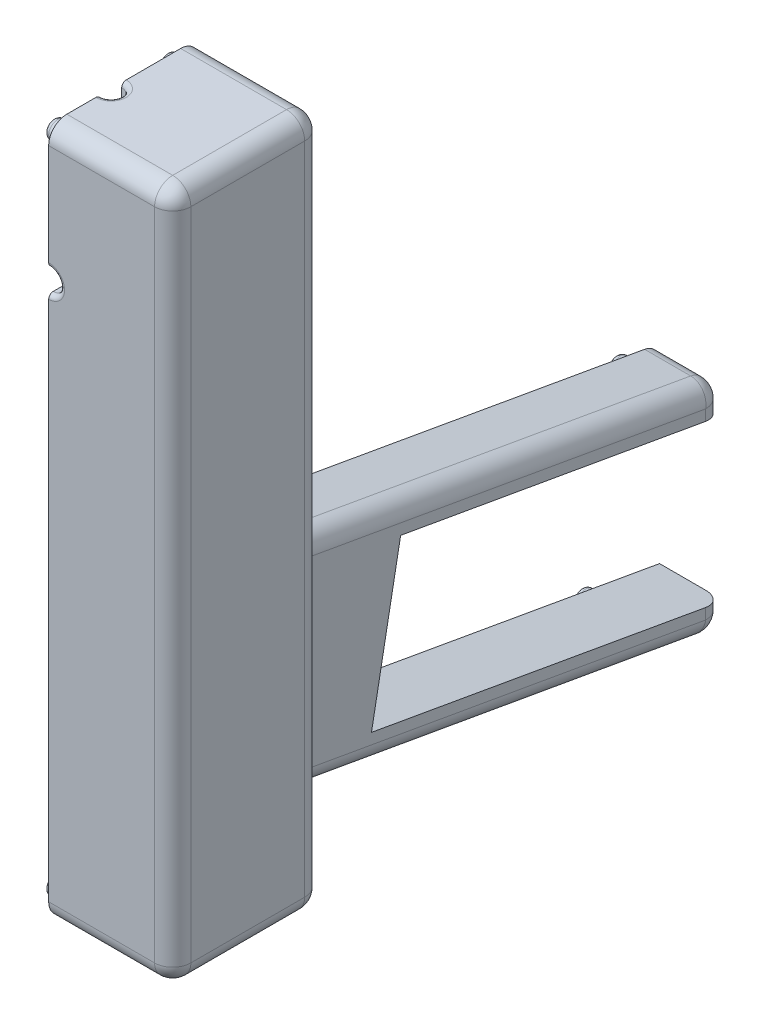
SolidWorks part; units mm, degrees
ref_plane "Front Plane" through (0, 0, 0) normal (0, 0, 1) x (1, 0, 0)
ref_plane "Top Plane" through (0, 0, 0) normal (0, 1, 0) x (1, 0, 0)
ref_plane "Right Plane" through (0, 0, 0) normal (1, 0, 0) x (0, 0, -1)
sketch "Sketch1" plane through (0, 0, 0) normal (0, 1, 0) x (1, 0, 0)
  line L1 (0, 0) -> (27.35, 0)
  line L2 (0, 0) -> (0, 33.1)
  line L3 (0, 33.1) -> (27.35, 33.1)
  line L4 (27.35, 0) -> (27.35, 33.1)
  dimension "D1" = 27.35
  dimension "D2" = 33.1
extrude "Boss-Extrude1" add sketch "Sketch1" along normal blind 152.4
sketch "Sketch2" plane through (0, 0, 0) normal (-1, 0, 0) x (0, 0, 1)
  line L0 (0, 152.4) -> (0, 0) construction
  line L1 (-6.35, 146.05) -> (-26.75, 146.05)
  line L2 (-6.35, 146.05) -> (-6.35, 6.35)
  line L3 (-6.35, 6.35) -> (-26.75, 6.35)
  line L4 (-26.75, 146.05) -> (-26.75, 6.35)
  line L5 (-33.1, 152.4) -> (0, 152.4) construction
  line L6 (-33.1, 152.4) -> (-33.1, 0) construction
  line L7 (-33.1, 0) -> (0, 0) construction
  dimension "D1" = 6.35
  dimension "D2" = 6.35
  dimension "D3" = 6.35
  dimension "D4" = 6.35
extrude "Cut-Extrude1" cut sketch "Sketch2" against normal blind 21
sketch "Sketch3" plane through (0, 0, 0) normal (0, 0, 1) x (1, 0, 0)
  line L0 (0, 152.4) -> (0, 0) construction
  line L1 (0, 125.055) -> (0, 120.055)
  arc A0 (0, 125.055) -> (0, 120.055) centre (0, 122.555) cw
  dimension "D1" = 29.845
extrude "HitLED" cut sketch "Sketch3" against normal up to next
sketch "Sketch6" plane through (21, 0, 0) normal (-1, 0, 0) x (0, 0, 1)
  line L0 (-15.7, 107.95) -> (-15.7, 33.02)
  line L1 (-9.35, 107.95) -> (-23.75, 107.95)
  line L2 (-9.35, 107.95) -> (-9.35, 33.02)
  line L3 (-9.35, 33.02) -> (-23.75, 33.02)
  line L4 (-23.75, 107.95) -> (-23.75, 33.02)
  line L5 (-17.4, 33.02) -> (-17.4, 107.95)
  line L7 (-6.35, 146.05) -> (-26.75, 146.05) construction
  line L8 (-26.75, 146.05) -> (-26.75, 6.35) construction
  line M8 (-6.35, 146.05) -> (-26.75, 146.05)
  dimension "D1" = 38.1
  dimension "D2" = 3
  dimension "D3" = 1.7
  dimension "D4" = 6.35
  dimension "D5" = 6.35
  dimension "D6" = 74.93
extrude "PCB" add sketch "Sketch6" along normal blind 6.35 contours L3 L2 L0 M8 | L3 L5 L1 L4
sketch "Sketch16" plane through (0, 0, 0) normal (-1, 0, 0) x (0, 0, 1)
  line L1 (-33.1, 152.4) -> (0, 152.4) construction
  line L2 (0, 120.055) -> (0, 0) construction
  line L3 (-33.1, 0) -> (0, 0) construction
  line L5 (-33.1, 152.4) -> (-33.1, 0) construction
  circle A0 centre (-4, 148.4) radius 2
  circle A1 centre (-4, 4) radius 2
  circle A2 centre (-29.1, 148.4) radius 2
  circle A3 centre (-29.1, 4) radius 2
  dimension "D1" = 4
  dimension "D3" = 4
  dimension "D2" = 4
  dimension "D4" = 4
extrude "PressFit" add sketch "Sketch16" along normal blind 3
fillet "Fillet-PressFit" radius 1 4 edges at (-3, 4, -27.1) (-3, 4, -2) (-3, 148.4, -27.1) (-3, 148.4, -2)
sketch "Sketch23" plane through (0, 0, -25.4) normal (-1, 0, 0) x (0, 0, 1)
  line L4 (-7.7, 61.1358) -> (-7.7, 12.7)
  line L5 (-7.7, 12.7) -> (-109.3, -5.2148)
  line L6 (-109.3, -5.2148) -> (-109.3, 43.221)
  line L7 (-109.3, 43.221) -> (-7.7, 61.1358)
  dimension "D1" = 47.7
  dimension "D2" = 12.7
extrude "Butt" add sketch "Sketch23" against normal blind 14.175
sketch "Sketch20" plane through (0, 0, 0) normal (-1, 0, 0) x (0, 0, 1)
  line L0 (-63.4356, 49.3389) -> (-57.0033, 14.9332)
  line L1 (-63.4356, 49.3389) -> (-130.4061, 37.5302)
  line L2 (-57.0033, 14.9332) -> (-123.9738, 3.1245)
  line L6 (-130.4061, 37.5302) -> (-134.7, 36.7731)
  line L10 (-123.9738, 3.1245) -> (-134.7, 1.2331)
  line L11 (-134.7, 1.2331) -> (-134.7, 36.7731)
  dimension "D2" = 35
extrude "BatteryPack" cut sketch "Sketch20" against normal blind 14.175
sketch "Sketch22" plane through (0, 0, 0) normal (-1, 0, 0) x (0, 0, 1)
  line L0 (-63.4356, 49.3389) -> (-134.7, 36.7731) construction
  line L2 (-134.7, 1.2331) -> (-57.0033, 14.9332) construction
  line L4 (-57.0033, 14.9332) -> (-63.4356, 49.3389) construction
  circle A0 centre (-128.067, 41.1666) radius 2
  circle A1 centre (-120.4429, 0.5231) radius 2
  dimension "D1" = 3.175
  dimension "D2" = 3.175
  dimension "D3" = 65.0325
  dimension "D4" = 65.0073
extrude "PressFit - Bottom" add sketch "Sketch22" along normal blind 3
sketch "Sketch25" plane through (0, 146.05, 0) normal (0, -1, 0) x (1, 0, 0)
  line L0 (0, -6.35) -> (0, -26.75) construction
  line L1 (0, -11.4) -> (0, -16.1)
  line L2 (21, -26.75) -> (0, -26.75) construction
  arc A0 (0, -11.4) -> (0, -16.1) centre (0, -13.75) cw
  dimension "D1" = 13
extrude "IRLED" cut sketch "Sketch25" against normal up to next
fillet "Fillet - Body" radius 4 17 edges at (14.175, -1.9908, -134.7) (14.175, 39.997, -134.7) (7.0875, 43.221, -134.7) (7.0875, -5.2148, -134.7) (14.175, 52.1784, -83.9) (14.175, 3.7426, -83.9) (7.0875, 12.7, -33.1) (14.175, 36.9179, -33.1) (7.0875, 61.1358, -33.1) (13.675, 152.4, -33.1) (13.675, 152.4, 0) (27.35, 152.4, -16.55) (27.35, 76.2, -33.1) (27.35, 0, -16.55) (13.675, 0, -33.1) (13.675, 0, 0) (27.35, 76.2, 0)
fillet "Fillet-PressFit-Bottom" radius 1 2 edges at (-3, 0.5231, -118.4429) (-3, 41.1666, -126.067)
fillet "Fillet-LED's" radius 1 2 edges at (2.35, 152.4, -13.75) (2.5, 122.555, 0)
sketch "Sketch26" plane through (0, 0, 0) normal (-1, 0, 0) x (0, 0, 1)
  line L0 (-46.718, 58.7346) -> (-53.6116, 57.5191)
  line L1 (-53.6116, 57.5191) -> (-52.9865, 53.9738)
  line L2 (-52.9865, 53.9738) -> (-46.0928, 55.1893)
  line L3 (-46.0928, 55.1893) -> (-46.718, 58.7346)
  line L4 (-36.4054, 60.553) -> (-131.3946, 43.8039) construction
  point P6 (-46.4054, 56.962)
  dimension "D1" = 3.6
  dimension "D2" = 7
  dimension "D3" = 10
  dimension "D4" = 0
extrude "Cut-Extrude2" cut sketch "Sketch26" against normal blind 3.5
sketch "Sketch27" plane through (0, 0, 0) normal (-1, 0, 0) x (0, 0, 1)
  line L0 (-40.1594, 56.2356) -> (-58.92, 52.9276)
  line L1 (-58.92, 52.9276) -> (-58.6248, 51.2534)
  line L2 (-58.6248, 51.2534) -> (-39.8642, 54.5614)
  line L3 (-39.8642, 54.5614) -> (-40.1594, 56.2356)
  line L6 (-52.9865, 53.9738) -> (-46.0928, 55.1893) construction
  line L7 (-46.0928, 55.1893) -> (-46.718, 58.7346) construction
  dimension "D1" = 1.7
  dimension "D2" = 19.05
  dimension "D3" = 6.025
extrude "Cut-Extrude3" cut sketch "Sketch27" against normal blind 12.065
sketch "Sketch28" plane through (0, 0, 0) normal (-1, 0, 0) x (0, 0, 1)
  line L0 (-43.3356, 53.9493) -> (-55.1533, 51.8655)
  line L1 (-43.3356, 53.9493) -> (-37.0756, 18.447)
  line L2 (-55.1533, 51.8655) -> (-48.8933, 16.3632)
  line L3 (-37.0756, 18.447) -> (-48.8933, 16.3632)
  line L4 (-58.6248, 51.2534) -> (-39.8642, 54.5614) construction
  line L5 (-39.8642, 54.5614) -> (-40.1594, 56.2356) construction
  dimension "D1" = 12
  dimension "D2" = 3.525
  dimension "D3" = 36.05
extrude "Cut-Extrude4" cut sketch "Sketch28" against normal blind 10.825
